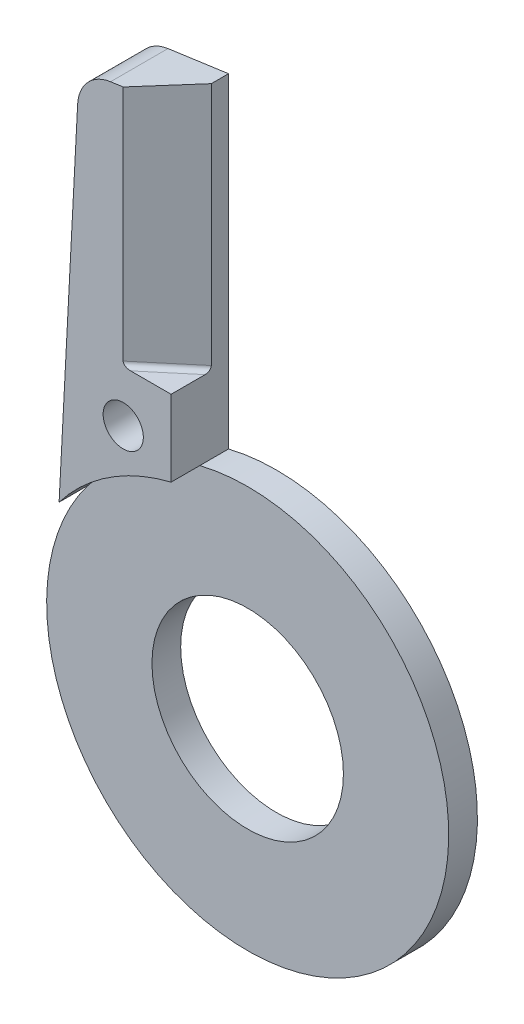
SolidWorks part; units mm, degrees
ref_plane "Alzado" through (0, 0, 0) normal (0, 0, 1) x (1, 0, 0)
ref_plane "Planta" through (0, 0, 0) normal (0, 1, 0) x (1, 0, 0)
ref_plane "Vista lateral" through (0, 0, 0) normal (1, 0, 0) x (0, 0, -1)
sketch "Croquis1" plane through (0, 0, 0) normal (0, 0, 1) x (1, 0, 0)
  line L0 (0, 54.2823) -> (0, 0) construction
  line L1 (-28.222, 0) -> (26.3028, 0) construction
  line L2 (-16.7, 12.7322) -> (-14.7622, 49.7072)
  line L3 (-11.3244, 53.4589) -> (-5, 54.3477)
  line L4 (-5, 54.3477) -> (-5, 20.3961)
  line L5 (0, 0) -> (0, -21) construction
  arc A0 (-16.7, 12.7322) -> (-5, 20.3961) centre (0, 0) ccw
  circle A1 centre (0, 0) radius 10
  arc A2 (-14.7622, 49.7072) -> (-11.3244, 53.4589) centre (-10.7677, 49.4978) cw
  point P14 (-14.5897, 53)
  dimension "D1" = 42
  dimension "D2" = 20
  dimension "D8" = 4
  dimension "D3" = 3
  dimension "D4" = 98
  dimension "D5" = 5
  dimension "D6" = 74
  dimension "D7" = 11.7
extrude "Saliente-Extruir1" add sketch "Croquis1" along normal blind 6
sketch "Croquis2" plane through (0, 0, 6) normal (0, 0, 1) x (1, 0, 0)
  circle A0 centre (0, 0) radius 21
  circle A1 centre (0, 0) radius 10
  arc A2 (-16.7, 12.7322) -> (-5, 20.3961) centre (0, 0) ccw construction
  circle A3 centre (0, 0) radius 10 construction
extrude "Cortar-Extruir1" cut sketch "Croquis2" against normal blind 3
ref_plane "Plano1" through (0, 54.3477, 0) normal (0, 1, 0) x (-1, 0, 0)
sketch "Croquis3" plane through (0, 54.3477, 0) normal (0, 1, 0) x (-1, 0, 0)
  line L0 (10.0054, 6) -> (5, 1.8)
  line L1 (5, 6) -> (11.3244, 6) construction
  line L2 (5, 6) -> (5, 0) construction
  line L3 (5, 1.8) -> (5, 6)
  line L4 (5, 6) -> (10.0054, 6)
  line L5 (5, 0) -> (11.3244, 0) construction
  dimension "D1" = 1.8
  dimension "D2" = 40
extrude "Cortar-Extruir2" cut sketch "Croquis3" against normal blind 26
fillet "Redondeo1" radius 0.5 1 edges at (-7.5027, 28.3477, 3.9)
hole_wizard "Taladro roscado M51" positions "Croquis5" profile "Croquis4" tap size "M5" standard "DIN"
sketch "Croquis5" plane through (0, 0, 6) normal (0, 0, 1) x (1, 0, 0)
  point P0 (-10, 23)
  dimension "D1" = 23
  dimension "D2" = 10
sketch "Croquis4" plane through (-10, 23, 6) normal (1, 0, 0) x (0, -1, 0)
  line L0 (0, 0) -> (0, 15.2618)
  line L1 (0, 15.2618) -> (2.1, 14)
  line L2 (2.1, 14) -> (2.1, 0)
  line L5 (2.1, 0) -> (0, 0)
  line L10 (0, 15.2618) -> (-2.1, 14) construction
  line L11 (0, -6.35) -> (0, 107.95) construction
  dimension "Diámetro de perforador para roscar" = 4.2
  dimension "Profundidad de perforador para roscar" = 14
  dimension "Ángulo de perforador" = 118
cosmetic thread "Rosca de taladro1" parameters "D1"=6, "D2"=5
